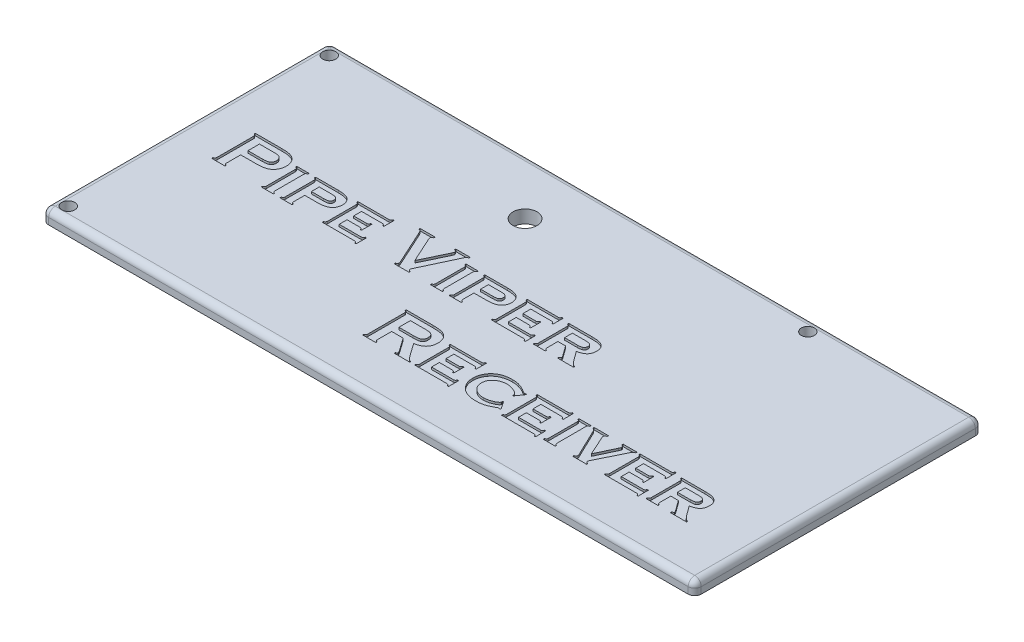
SolidWorks part; units mm, degrees
ref_plane "Front Plane" through (0, 0, 0) normal (0, 0, 1) x (1, 0, 0)
ref_plane "Top Plane" through (0, 0, 0) normal (0, 1, 0) x (1, 0, 0)
ref_plane "Right Plane" through (0, 0, 0) normal (1, 0, 0) x (0, 0, -1)
sketch "Sketch1" plane through (0, 0, 0) normal (0, 1, 0) x (1, 0, 0)
  line L1 (-75, -33) -> (75, -33)
  line L2 (-75, -33) -> (-75, 33)
  line L3 (-75, 33) -> (75, 33)
  line L4 (75, -33) -> (75, 33)
  line L5 (-75, -33) -> (75, 33) construction
  line L6 (-75, 33) -> (75, -33) construction
  point P0 (0, 0)
  dimension "D1" = 66
  dimension "D2" = 150
extrude "Boss-Extrude1" add sketch "Sketch1" along normal blind 3
fillet "Fillet1" radius 1.5 8 edges at (0, 3, 33) (-75, 3, 0) (0, 3, -33) (75, 3, 0) (75, 1.5, -33) (75, 1.5, 33) (-75, 1.5, -33) (-75, 1.5, 33)
sketch "Sketch2" plane through (0, 0, 0) normal (0, -1, 0) x (1, 0, 0)
  circle A0 centre (-72, 30) radius 1.5 construction
  circle A1 centre (-72, 30) radius 1.5
  circle A2 centre (-72, -30) radius 1.5 construction
  circle A3 centre (-72, -30) radius 1.5
  circle A4 centre (38, -30) radius 1.5 construction
  circle A5 centre (38, -30) radius 1.5
extrude "Cut-Extrude1" cut sketch "Sketch2" against normal through all both and the other way through all
sketch "Sketch3" plane through (0, 3, 0) normal (0, 1, 0) x (1, 0, 0)
  line L0 (38, 30) -> (38, -26) construction
  line L1 (38, 30) -> (38, -26) construction
  line L2 (-72, 30) -> (38, 30) construction
  line L3 (-72, 30) -> (38, 30) construction
  circle A0 centre (-17, 20) radius 2.75
  dimension "D3" = 5.5
  dimension "D1" = 55
  dimension "D2" = 10
extrude "Cut-Extrude2" cut sketch "Sketch3" against normal through all both
sketch "Sketch4" plane through (0, 3, 0) normal (0, 1, 0) x (1, 0, 0)
  line L0 (-73.5, -4) -> (73.5, -4) construction
  line L1 (-73.5, 30) -> (-73.5, -30) construction
  line L2 (73.5, -31.5) -> (73.5, 31.5) construction
  line L3 (-72, -31.5) -> (73.5, -31.5) construction
  text T0 "  Pipe Viper\r\n                Receiver" font "Copperplate Gothic Bold" height 10
  point P7 (0, 0)
  dimension "D1" = 27.5
extrude "Cut-Extrude3" cut sketch "Sketch4" against normal blind 0.5
